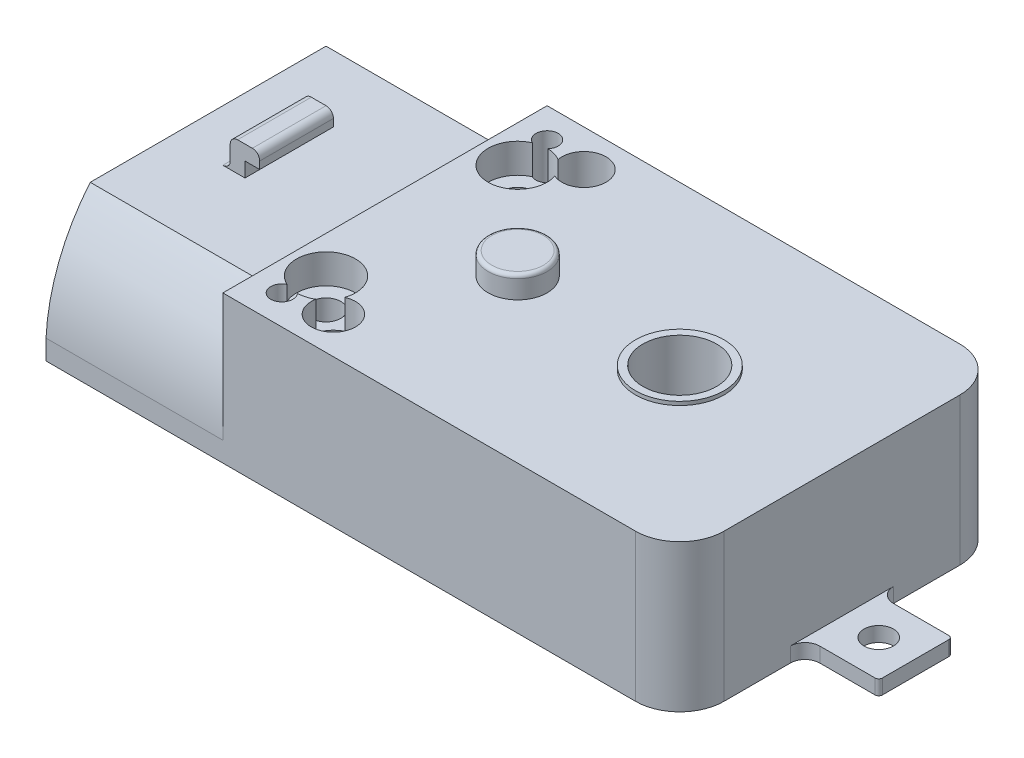
SolidWorks part; units mm, degrees
ref_plane "Front Plane" through (0, 0, 0) normal (0, 0, 1) x (1, 0, 0)
ref_plane "Top Plane" through (0, 0, 0) normal (0, 1, 0) x (1, 0, 0)
ref_plane "Right Plane" through (0, 0, 0) normal (1, 0, 0) x (0, 0, -1)
sketch "Sketch2" plane through (0, 0, 0) normal (0, 1, 0) x (1, 0, 0)
  line L0 (31, 11) -> (0, 11) construction
  line L1 (0, 0) -> (31, 0)
  line L2 (0, 0) -> (0, 22)
  line L3 (0, 22) -> (31, 22)
  line L4 (31, 0) -> (31, 22)
  line L7 (31, 8.5) -> (31, 13.5)
  dimension "48" = 31
  dimension "22" = 22
extrude "Boss-Extrude2" add sketch "Sketch2" along normal blind 9 contours L0 L7 L4 L3 L2 | L4 L0 L2 L1
sketch "Sketch4" plane through (31, 0, 0) normal (1, 0, 0) x (0, 0, -1)
  line L0 (0, 0) -> (22, 0) construction
  line L1 (8.5, 0) -> (13.5, 0)
  line L2 (8.5, 0) -> (8.5, 1)
  line L3 (8.5, 1) -> (13.5, 1)
  line L4 (13.5, 0) -> (13.5, 1)
  point P6 (11, 1)
  dimension "D1" = 1
  dimension "D2" = 5
  dimension "D3" = 11
extrude "Boss-Extrude3" add sketch "Sketch4" along normal blind 5
sketch "Sketch5" plane through (0, 1, 0) normal (0, 1, 0) x (1, 0, 0)
  circle A0 centre (33.5, 11) radius 1
  dimension "D1" = 2
  dimension "D2" = 2.5
  dimension "D3" = 2.5
extrude "Cut-Extrude1" cut sketch "Sketch5" against normal blind 5
fillet "Fillet1" radius 1 1 edges
fillet "Fillet2" radius 1 1 edges
fillet "Fillet3" radius 3 1 edges at (31, 4.5, 0)
fillet "Fillet4" radius 3 1 edges at (31, 4.5, -22)
sketch "Sketch6" plane through (0, 0, 0) normal (-1, 0, 0) x (0, 0, 1)
  line L0 (-11, 0) -> (-11, 9) construction
  line L1 (0, 0) -> (-22, 0) construction
  line L2 (0, 9) -> (-22, 9) construction
  line L3 (-22, 0) -> (0, 0)
  line L5 (-22, 0) -> (-22.0206, -0.0102)
  line L6 (0, 1.3449) -> (0, 0)
  line L7 (-19, 9) -> (-3, 9)
  line L8 (0, 0) -> (-22, 0)
  arc A0 (0, 0) -> (-3, 9) centre (-12.9826, 0.6725) ccw
  arc A1 (-22, 0) -> (-19, 9) centre (-9.0174, 0.6725) cw
  point P9 (0, 0)
  line M1 (-22, 0) -> (0, 0)
  line M2 (0, 0) -> (0, 9)
  line M3 (0, 9) -> (-22, 9)
  line M4 (-22, 9) -> (-22, 0)
  dimension "D1" = 13
  dimension "D2" = 3
sketch "Sketch7" plane through (0, 0, 0) normal (-1, 0, 0) x (0, 0, 1)
extrude "Boss-Extrude4" add sketch "Sketch6" along normal blind 12 contours L0 L7 A1 M1 M4 | L0 L8 A0 M2 M3
fillet "Fillet6" radius 0.25 2 edges at (36, 0.5, -13.5) (36, 0.5, -8.5)
sketch "Sketch10" plane through (0, 9, 0) normal (0, 1, 0) x (1, 0, 0)
  line L0 (-12, 11) -> (30.5, 11) construction
  line L1 (-12, 3) -> (-12, 19) construction
  line L2 (30.5, 3) -> (30.5, 19) construction
  line L4 (28, 0) -> (0, 0) construction
  circle A0 centre (5, 19.5) radius 1.5
  circle A1 centre (5, 2.5) radius 1.5
  dimension "D1" = 3
  dimension "2,5" = 2.5
  dimension "5" = 5
extrude "Cut-Extrude7" cut sketch "Sketch10" against normal through all both and the other way through all
sketch "Sketch12" plane through (0, 9, 0) normal (0, 1, 0) x (1, 0, 0)
  line L0 (28, 0) -> (0, 0) construction
  circle A0 centre (2, 2) radius 0.75
  circle A1 centre (2, 20) radius 0.75
  dimension "D1" = 1.5
  dimension "D2" = 1.5
  dimension "D3" = 2
  dimension "D4" = 2
  dimension "D5" = 2
  dimension "D6" = 2
extrude "Cut-Extrude8" cut sketch "Sketch12" against normal blind 3
sketch "Sketch13" plane through (0, 9, 0) normal (0, 1, 0) x (1, 0, 0)
  line L0 (-12, 11) -> (36, 11) construction
  line L1 (-8, 13.5) -> (-7, 13.5)
  line L2 (-8, 13.5) -> (-8, 8.5)
  line L3 (-8, 8.5) -> (-7, 8.5)
  line L4 (-7, 13.5) -> (-7, 8.5)
  line L5 (-12, 3) -> (-12, 19) construction
  line L6 (36, 13.25) -> (36, 8.75) construction
  dimension "D1" = 4
  dimension "D2" = 1
  dimension "D3" = 5
  dimension "D4" = 2.5
extrude "Boss-Extrude5" add sketch "Sketch13" along normal blind 2
sketch "Sketch14" plane through (-7, 0, 0) normal (1, 0, 0) x (0, 0, -1)
  line L0 (13.5, 11) -> (13.5, 9) construction
  line L1 (8.5, 11) -> (13.5, 11)
  line L2 (8.5, 11) -> (8.5, 10)
  line L3 (8.5, 10) -> (13.5, 10)
  line L4 (13.5, 11) -> (13.5, 10)
extrude "Boss-Extrude6" add sketch "Sketch14" along normal blind 1
fillet "Fillet7" radius 0.5 1 edges at (-8, 11, -11)
fillet "Fillet8" radius 0.5 1 edges at (-8, 9, -11)
fillet "Fillet9" radius 0.5 1 edges at (-6, 11, -11)
sketch "Sketch16" plane through (-12, 0, 0) normal (-1, 0, 0) x (0, 0, 1)
  line L0 (-18.2321, 8.3594) -> (-3.7679, 8.3594)
  line L1 (-21.0013, 1.2932) -> (-21, 0)
  line L2 (-0.9987, 1.2932) -> (-0.9987, 0)
  line L3 (-21, 0) -> (-0.9987, 0)
  arc A2 (-18.2321, 8.3594) -> (-21.0013, 1.2932) centre (-9.0174, 0.6725) ccw
  arc A3 (-18.2321, 8.3594) -> (-21.0013, 1.2932) centre (-9.0174, 0.6725) ccw
  arc A5 (-0.9987, 1.2932) -> (-3.7679, 8.3594) centre (-12.9826, 0.6725) ccw
  arc A6 (-0.9987, 1.2932) -> (-3.7679, 8.3594) centre (-12.9826, 0.6725) ccw
  dimension "D1" = 1
  dimension "D2" = 1
extrude "Cut-Extrude9" cut sketch "Sketch16" against normal blind 10
sketch "Sketch17" plane through (0, 9, 0) normal (0, 1, 0) x (1, 0, 0)
  line L0 (0, 3) -> (0, 19)
  line L8 (31, 3) -> (31, 19)
  line L9 (28, 22) -> (0, 22)
  line L10 (0, 22) -> (0, 19)
  line L11 (0, 19) -> (-12, 19)
  line L12 (-12, 19) -> (-12, 3)
  line L13 (-12, 3) -> (0, 3)
  line L14 (0, 3) -> (0, 0)
  line L15 (0, 0) -> (28, 0)
  line L16 (31, 3) -> (31, 19)
  line L17 (28, 22) -> (0, 22)
  line L18 (0, 22) -> (0, 19)
  line L22 (0, 3) -> (0, 0)
  line L23 (0, 0) -> (28, 0)
  arc A2 (31, 19) -> (28, 22) centre (28, 19) ccw
  arc A3 (28, 0) -> (31, 3) centre (28, 3) ccw
  arc A4 (31, 19) -> (28, 22) centre (28, 19) ccw
  arc A5 (28, 0) -> (31, 3) centre (28, 3) ccw
  dimension "D1" = 0
extrude "Boss-Extrude7" add sketch "Sketch17" along normal blind 1
sketch "Sketch18" plane through (0, 10, 0) normal (0, 1, 0) x (1, 0, 0)
  line L0 (0, 11) -> (31, 11) construction
  line L1 (0, 19) -> (0, 3) construction
  line L2 (31, 3) -> (31, 19) construction
  circle A1 centre (5, 19.5) radius 1.5
  circle A3 centre (5, 2.5) radius 1.5
  dimension "D3" = 2.5
  dimension "D8" = 5
  dimension "3" = 3
  dimension "D10" = 3
  dimension "D2" = 2.5
  dimension "D9" = 5
extrude "Cut-Extrude12" cut sketch "Sketch18" against normal through all
sketch "Sketch19" plane through (0, 10, 0) normal (0, 1, 0) x (1, 0, 0)
  line L0 (0, 11) -> (31, 11) construction
  line L1 (0, 22) -> (0, 0) construction
  line L2 (31, 3) -> (31, 19) construction
  circle A0 centre (2, 20) radius 0.75
  circle A1 centre (2, 2) radius 0.75
  dimension "D1" = 1.5
  dimension "D2" = 1.5
  dimension "D3" = 2
  dimension "2" = 2
  dimension "D4" = 2
  dimension "D5" = 2
extrude "Cut-Extrude14" cut sketch "Sketch19" against normal through all
sketch "Sketch20" plane through (0, 10, 0) normal (0, 1, 0) x (1, 0, 0)
  line L0 (0, 11) -> (31, 11) construction
  line L1 (0, 22) -> (0, 0) construction
  line L2 (31, 3) -> (31, 19) construction
  circle A0 centre (9, 11) radius 2
  dimension "D2" = 4
  dimension "D1" = 22
extrude "Boss-Extrude8" add sketch "Sketch20" along normal blind 1.5
fillet "Fillet10" radius 0.25 1 edges at (9, 11.5, -9)
sketch "Sketch21" plane through (0, 10, 0) normal (0, 1, 0) x (1, 0, 0)
  line L0 (0, 11) -> (31, 11) construction
  line L1 (0, 19) -> (0, 3) construction
  line L2 (31, 3) -> (31, 19) construction
  circle A0 centre (20, 11) radius 2.5
  dimension "D1" = 11
  dimension "6" = 5
extrude "Cut-Extrude15" cut sketch "Sketch21" against normal blind 5
sketch "Sketch22" plane through (0, 10, 0) normal (0, 1, 0) x (1, 0, 0)
  circle A0 centre (20, 11) radius 3
  circle A1 centre (20, 11) radius 2.5
  dimension "D1" = 6
  dimension "D2" = 5
extrude "Boss-Extrude9" add sketch "Sketch22" along normal blind 0.25
sketch "Sketch24" plane through (0, 10, 0) normal (0, 1, 0) x (1, 0, 0)
  line L0 (0, 11) -> (36, 11) construction
  line L1 (0, 19) -> (0, 3) construction
  line L2 (36, 13.25) -> (36, 8.75) construction
  circle A0 centre (2.5, 17.5) radius 2
  circle A1 centre (2.5, 4.5) radius 2
  dimension "D1" = 4
  dimension "D2" = 2.5
  dimension "D3" = 4.5
extrude "Cut-Extrude16" cut sketch "Sketch24" against normal blind 2
sketch "Sketch25" plane through (0, 10, 0) normal (0, 1, 0) x (1, 0, 0)
  circle A0 centre (2.5, 17.5) radius 1
  circle A1 centre (2.5, 4.5) radius 1
  dimension "D1" = 2
  dimension "D2" = 2
extrude "Cut-Extrude17" cut sketch "Sketch25" against normal blind 5
